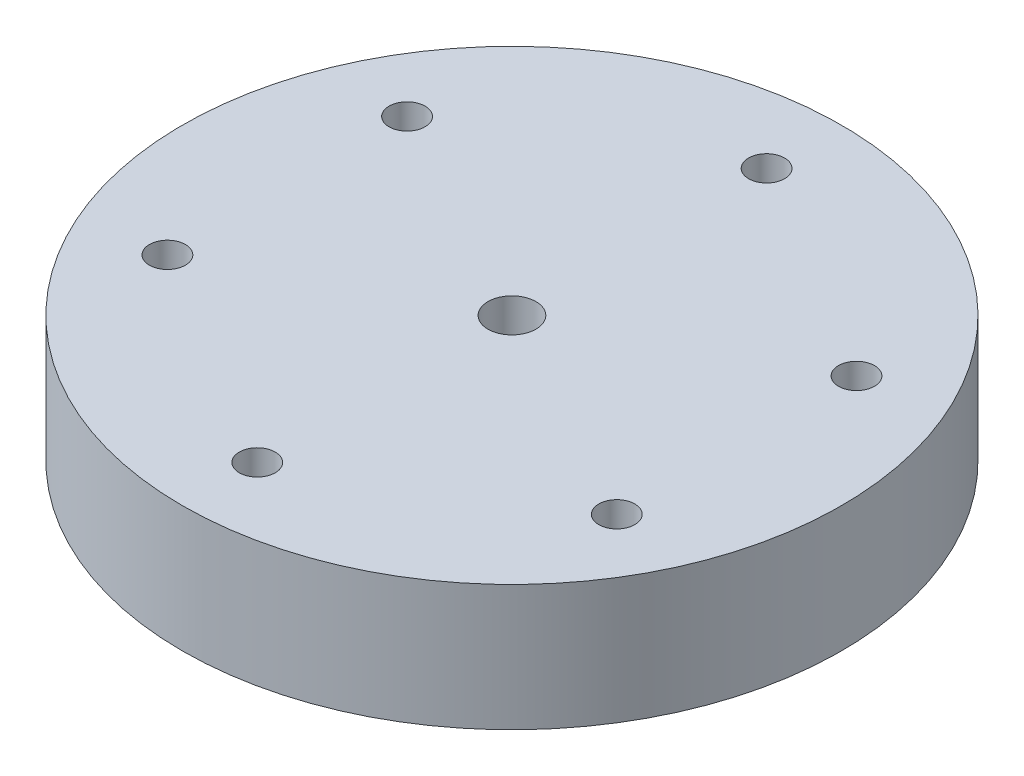
SolidWorks part; units mm, degrees
ref_plane "Front Plane" through (0, 0, 0) normal (0, 0, 1) x (1, 0, 0)
ref_plane "Top Plane" through (0, 0, 0) normal (0, 1, 0) x (1, 0, 0)
ref_plane "Right Plane" through (0, 0, 0) normal (1, 0, 0) x (0, 0, -1)
sketch "Sketch1" plane through (0, 0, 0) normal (0, 1, 0) x (1, 0, 0)
  circle A0 centre (0, 0) radius 55
  circle A1 centre (0, 0) radius 4
  dimension "D1" = 110
  dimension "D2" = 8
extrude "Boss-Extrude1" add sketch "Sketch1" along normal blind 21
sketch "Sketch2" plane through (0, 0, 0) normal (0, 1, 0) x (1, 0, 0)
  line L0 (-37.5, 0) -> (37.5, 0) construction
  line L1 (0, 0) -> (0, 55) construction
  line L2 (-37.5, -20) -> (-37.5, 20) construction
  line L3 (37.5, -20) -> (37.5, 20) construction
  line L4 (0, 0) -> (0, 42.5) construction
  circle A0 centre (0, 0) radius 55 construction
  circle A1 centre (-37.5, 20) radius 3
  circle A2 centre (-37.5, -20) radius 3
  circle A3 centre (37.5, -20) radius 3
  circle A4 centre (37.5, 20) radius 3
  circle A5 centre (0, 42.5) radius 3
  circle A6 centre (0, -42.5) radius 3
  point P15 (0, -42.5)
  dimension "D2" = 6
  dimension "D5" = 6
  dimension "D6" = 6
  dimension "D1" = 75
  dimension "D3" = 40
  dimension "D4" = 42.5
extrude "Cut-Extrude3" cut sketch "Sketch2" against normal blind 10 and the other way through all contours A4 | A3 | A2 | A1 | A5 | A6
sketch "Sketch3" plane through (0, 0, 0) normal (0, 1, 0) x (1, 0, 0)
  line L0 (37.5, -20) -> (37.5, 20) construction
  line L1 (-37.5, -20) -> (-37.5, 20) construction
  line L2 (-37.5, 0) -> (37.5, 0) construction
  line L3 (37.5, -20) -> (37.5, 20) construction
  line L4 (-37.5, -20) -> (-37.5, 20) construction
  line L5 (-37.5, 0) -> (37.5, 0) construction
  line L6 (0, 0) -> (0, 55) construction
  line L7 (0, 0) -> (0, 55) construction
  circle A0 centre (-37.5, 20) radius 5
  circle A1 centre (-37.5, -20) radius 5
  circle A2 centre (37.5, 20) radius 5
  circle A3 centre (37.5, -20) radius 5
  circle A4 centre (0, 42.5) radius 5
  circle A5 centre (0, -42.5) radius 5
  point P12 (0, 42.5)
  point P14 (0, -42.5)
  dimension "D1" = 10
  dimension "D2" = 10
  dimension "D3" = 10
extrude "Cut-Extrude4" cut sketch "Sketch3" along normal blind 6
